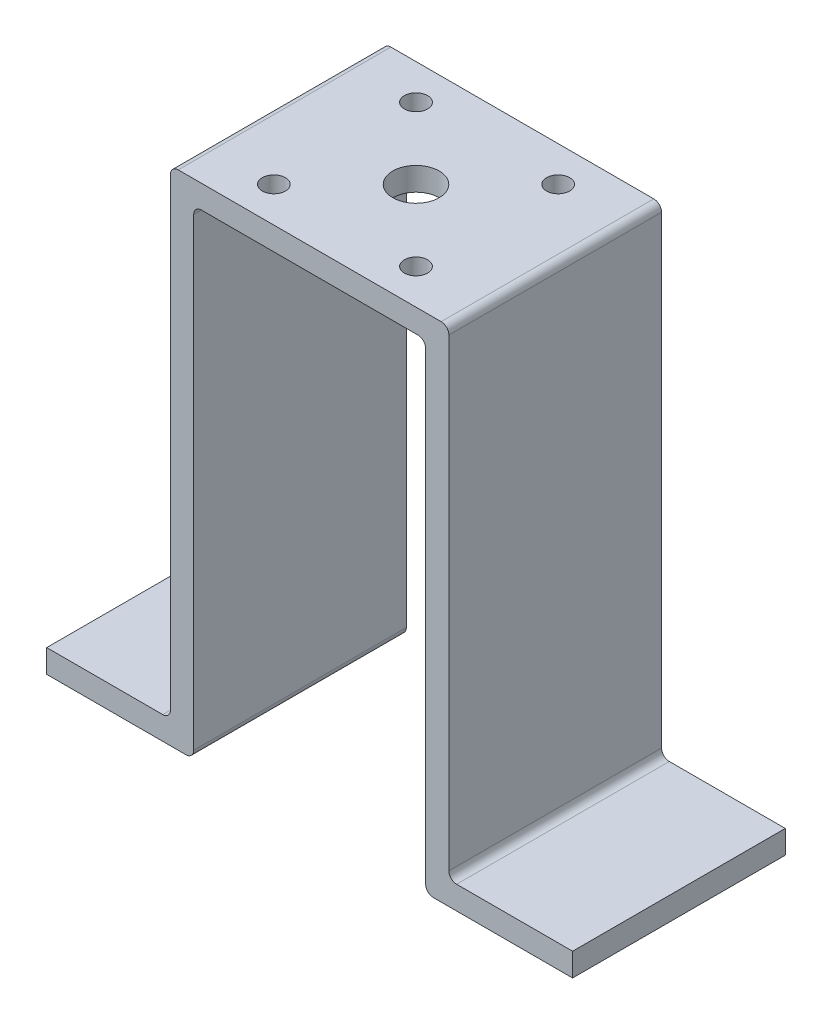
SolidWorks part; units mm, degrees
ref_plane "Front Plane" through (0, 0, 0) normal (0, 0, 1) x (1, 0, 0)
ref_plane "Top Plane" through (0, 0, 0) normal (0, 1, 0) x (1, 0, 0)
ref_plane "Right Plane" through (0, 0, 0) normal (1, 0, 0) x (0, 0, -1)
sketch "Sketch1" plane through (0, 0, 0) normal (0, 0, 1) x (1, 0, 0)
  line L0 (0, 37.295) -> (0, -24.705) construction
  line L1 (0, 37.295) -> (-14, 37.295)
  line L2 (-15, 36.295) -> (-15, -23.705)
  line L3 (-16, -24.705) -> (-34, -24.705)
  line L4 (-34, -24.705) -> (-34, -21.705)
  line L5 (-34, -21.705) -> (-19, -21.705)
  line L6 (-18, -20.705) -> (-18, 39.295)
  line L7 (-17, 40.295) -> (0, 40.295)
  line L8 (0, 40.295) -> (0, 37.295)
  arc A0 (-15, -23.705) -> (-16, -24.705) centre (-16, -23.705) cw
  arc A1 (-14, 37.295) -> (-15, 36.295) centre (-14, 36.295) ccw
  arc A2 (-18, 39.295) -> (-17, 40.295) centre (-17, 39.295) cw
  arc A3 (-19, -21.705) -> (-18, -20.705) centre (-19, -20.705) ccw
  point P10 (-15, 37.295)
  dimension "D3" = 1
  dimension "D7" = 1
  dimension "D1" = 15
  dimension "D2" = 34
  dimension "D4" = 3
  dimension "D5" = 3
  dimension "D6" = 3
  dimension "D8" = 62
extrude "Boss-Extrude1" add sketch "Sketch1" along normal mid plane 27.5
mirror "Mirror1" about plane through (0, 0, 0) normal (1, 0, 0) of "Boss-Extrude1"
sketch "Sketch2" plane through (0, 40.295, 0) normal (0, 1, 0) x (1, 0, 0)
  line L1 (-9.19, -9.19) -> (9.19, -9.19) construction
  line L2 (-9.19, -9.19) -> (-9.19, 9.19) construction
  line L3 (-9.19, 9.19) -> (9.19, 9.19) construction
  line L4 (9.19, -9.19) -> (9.19, 9.19) construction
  line L5 (-9.19, -9.19) -> (9.19, 9.19) construction
  line L6 (-9.19, 9.19) -> (9.19, -9.19) construction
  circle A0 centre (0, 0) radius 3
  circle A1 centre (-9.19, 9.19) radius 1.5
  circle A2 centre (9.19, 9.19) radius 1.5
  circle A3 centre (9.19, -9.19) radius 1.5
  circle A4 centre (-9.19, -9.19) radius 1.5
  dimension "D1" = 6
  dimension "D4" = 3
  dimension "D5" = 3
  dimension "D6" = 3
  dimension "D7" = 3
  dimension "D2" = 18.38
  dimension "D3" = 18.38
extrude "Cut-Extrude1" cut sketch "Sketch2" against normal through all
